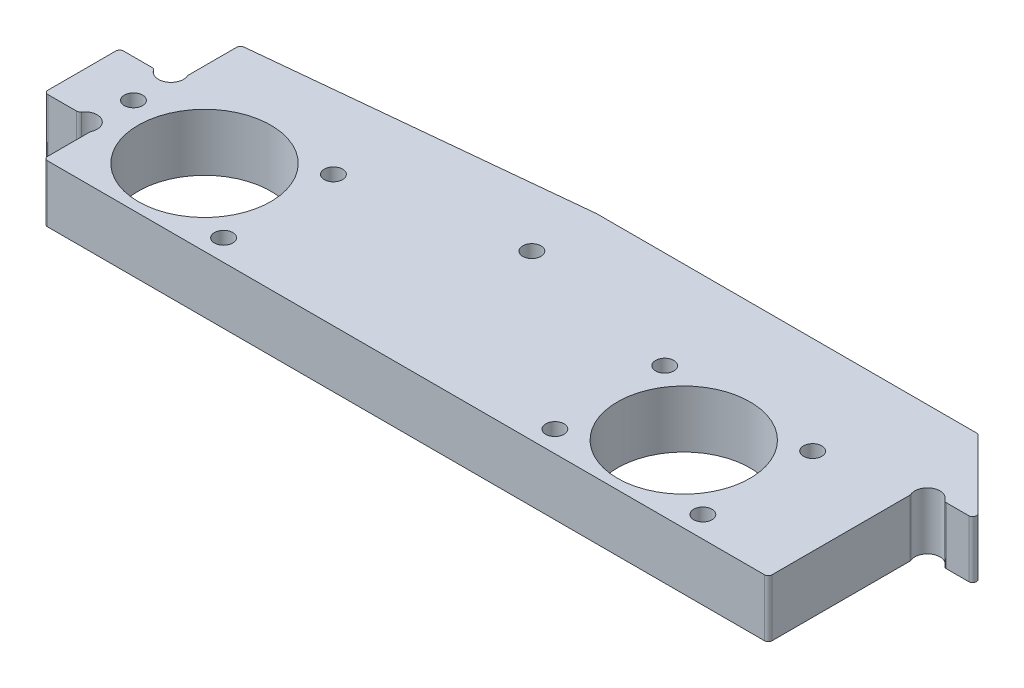
SolidWorks part; units mm, degrees
material "PE High Density"
ref_plane "Front Plane" through (0, 0, 0) normal (0, 0, 1) x (1, 0, 0)
ref_plane "Top Plane" through (0, 0, 0) normal (0, 1, 0) x (1, 0, 0)
ref_plane "Right Plane" through (0, 0, 0) normal (1, 0, 0) x (0, 0, -1)
sketch "Sketch1" plane through (0, 0, 0) normal (0, 1, 0) x (1, 0, 0)
  line L1 (-63.5, -19.05) -> (63.5, -19.05)
  line L2 (-63.5, -19.05) -> (-63.5, 19.05)
  line L3 (-63.5, 19.05) -> (63.5, 19.05)
  line L4 (63.5, -19.05) -> (63.5, 19.05)
  line L5 (-63.5, -19.05) -> (63.5, 19.05) construction
  line L6 (-63.5, 19.05) -> (63.5, -19.05) construction
  point P0 (0, 0)
  dimension "D1" = 127
  dimension "D2" = 38.1
extrude "Boss-Extrude1" add sketch "Sketch1" along normal blind 9.525
sketch "Sketch3" plane through (0, 0, 0) normal (0, -1, 0) x (1, 0, 0)
  line L0 (0, -19.05) -> (-63.5, -12.7)
  line L1 (63.5, -19.05) -> (-63.5, -19.05) construction
  line L2 (-63.5, -19.05) -> (-63.5, 19.05) construction
  line L3 (-63.5, -12.7) -> (-63.5, -19.05)
  line L4 (-63.5, -19.05) -> (0, -19.05)
  dimension "D1" = 6.35
extrude "Cut-Extrude2" cut sketch "Sketch3" against normal through all
sketch "Sketch4" plane through (0, 9.525, 0) normal (0, 1, 0) x (1, 0, 0)
  line L0 (-63.5, -6.35) -> (-39.9034, -6.35) construction
  line L1 (-63.5, 12.7) -> (-63.5, -19.05) construction
  line L2 (-39.9034, -6.35) -> (-39.9034, -19.05) construction
  line L3 (-63.5, -19.05) -> (63.5, -19.05) construction
  line L4 (39.9034, -6.35) -> (39.9034, -19.05) construction
  line L5 (39.9034, -6.35) -> (63.5, -6.35) construction
  line L6 (63.5, -19.05) -> (63.5, 19.05) construction
  circle A0 centre (-39.9034, -6.35) radius 2.2225
  circle A1 centre (39.9034, -6.35) radius 2.2225
  dimension "D3" = 4.445
  dimension "D1" = 12.7
  dimension "D2" = 23.5966
extrude "Cut-Extrude3" cut sketch "Sketch4" against normal through all
sketch "Sketch5" plane through (0, 9.525, 0) normal (0, 1, 0) x (1, 0, 0)
  circle A0 centre (-39.9034, -6.35) radius 3.1115
  circle A1 centre (39.9034, -6.35) radius 3.1115
  dimension "D1" = 6.223
extrude "Cut-Extrude4" cut sketch "Sketch5" against normal blind 2.5
sketch "Sketch7" plane through (0, 0, 0) normal (0, -1, 0) x (1, 0, 0)
  line L0 (58.7375, -14.2875) -> (58.7375, 14.2875) construction
  line L1 (58.7375, 14.2875) -> (-58.7375, 14.2875) construction
  line L2 (-58.7375, 14.2875) -> (-58.7375, -7.9375) construction
  line L3 (63.5, 14.2875) -> (58.7375, 14.2875) construction
  line L4 (63.5, 19.05) -> (63.5, -19.05) construction
  line L5 (58.7375, 14.2875) -> (58.7375, 19.05) construction
  line L6 (-63.5, 19.05) -> (63.5, 19.05) construction
  line L7 (-58.7375, 14.2875) -> (-63.5, 14.2875) construction
  line L8 (-63.5, -12.7) -> (-63.5, 19.05) construction
  line L9 (58.7375, -14.2875) -> (58.7375, -19.05) construction
  line L10 (63.5, -19.05) -> (0, -19.05) construction
  line L11 (-63.5, -12.7) -> (-58.7375, -12.7) construction
  line L12 (-58.7375, -12.7) -> (-58.7375, -7.9375) construction
  circle A0 centre (58.7375, 14.2875) radius 1.3891 construction
  circle A1 centre (58.7375, -14.2875) radius 1.3891 construction
  circle A2 centre (-58.7375, -7.9375) radius 1.3891
  circle A3 centre (-58.7375, 14.2875) radius 1.3891
  dimension "D1" = 2.7781
  dimension "D2" = 4.7625
extrude "Cut-Extrude6" cut sketch "Sketch7" against normal through all
sketch "Sketch8" plane through (0, 9.525, 0) normal (0, 1, 0) x (1, 0, 0)
  circle A0 centre (-39.9034, -6.35) radius 11.0363
  circle A1 centre (39.9034, -6.35) radius 11.0363
  dimension "D1" = 22.0726
extrude "Cut-Extrude7" cut sketch "Sketch8" against normal through all
sketch "Sketch9" plane through (0, 9.525, 0) normal (0, 1, 0) x (1, 0, 0)
  line L5 (0, 8.255) -> (0, 19.05) construction
  circle A6 centre (0, 8.255) radius 1.524
  dimension "D1" = 3.048
  dimension "D3" = 10.795
extrude "Cut-Extrude8" cut sketch "Sketch9" against normal through all
sketch "Sketch10" plane through (0, 9.525, 0) normal (0, 1, 0) x (1, 0, 0)
  line L6 (63.5, -19.05) -> (63.5, 19.05)
  line L7 (63.5, 19.05) -> (76.2, 6.35)
  line L8 (76.2, 6.35) -> (76.2, -19.05)
  line L9 (76.2, -19.05) -> (63.5, -19.05)
  dimension "D1" = 12.7
  dimension "D2" = 45
extrude "Boss-Extrude3" add sketch "Sketch10" against normal through all
sketch "Sketch11" plane through (0, 9.525, 0) normal (0, 1, 0) x (1, 0, 0)
  line L0 (71.4375, -19.05) -> (71.4375, -14.2875) construction
  line L1 (-63.5, -19.05) -> (76.2, -19.05) construction
  line L2 (71.4375, -14.2875) -> (76.2, -14.2875) construction
  line L3 (76.2, -19.05) -> (76.2, 6.35) construction
  line L4 (76.2, 1.5875) -> (71.4375, 1.5875) construction
  line L5 (71.4375, 1.5875) -> (71.4375, 6.35) construction
  line L6 (-58.7375, -14.2875) -> (-58.7375, -19.05) construction
  circle A0 centre (71.4375, 1.5875) radius 1.3891
  circle A1 centre (71.4375, -14.2875) radius 1.3891
  circle A2 centre (-58.7375, -14.2875) radius 1.3891 construction
extrude "Cut-Extrude9" cut sketch "Sketch11" against normal through all
sketch "Sketch13" plane through (0, 9.525, 0) normal (0, 1, 0) x (1, 0, 0)
  line L1 (-63.5, -19.05) -> (-53.975, -19.05)
  line L2 (-63.5, -19.05) -> (-63.5, -14.2875)
  line L3 (-63.5, 12.7) -> (-53.975, 12.7) construction
  line L5 (-63.5, -19.05) -> (-53.975, 12.7) construction
  line L6 (-63.5, 12.7) -> (-53.975, -19.05) construction
  line L7 (-58.7375, -14.2875) -> (-58.7375, -3.175) construction
  line L8 (-63.5, -14.2875) -> (-50.8, -14.2875) construction
  line L9 (-63.5, 12.7) -> (-63.5, 3.1115)
  line L10 (-63.5, 12.7) -> (-63.5, -19.05) construction
  line L11 (-63.5, 3.1115) -> (-53.975, 3.1115)
  line L12 (-53.975, 3.1115) -> (-53.975, 12.7)
  line L13 (-53.975, -19.05) -> (-53.975, -9.4615)
  line L14 (-53.975, -9.4615) -> (-63.5, -9.4615)
  line L15 (-63.5, -9.4615) -> (-63.5, -14.2875)
  line L16 (0, 19.05) -> (-63.5, 12.7) construction
  line L17 (-53.975, 12.7) -> (-53.975, 13.6525)
  line L18 (-53.975, 13.6525) -> (-63.5, 12.7)
  point P4 (-58.7375, -3.175)
  dimension "D1" = 12.7
  dimension "D2" = 12.573
extrude "Cut-Extrude10" cut sketch "Sketch13" against normal through all
sketch "Sketch14" plane through (0, 9.525, 0) normal (0, 1, 0) x (1, 0, 0)
  line L0 (-53.975, 3.1115) -> (-55.8605, 4.0259) construction
  line L1 (-55.8605, 4.0259) -> (-53.975, 4.9403) construction
  line L2 (-53.975, 3.1115) -> (-53.975, 13.6525) construction
  line L3 (-53.975, -9.4615) -> (-55.8605, -10.3759) construction
  line L4 (-55.8605, -10.3759) -> (-53.975, -11.2903) construction
  line L5 (-53.975, -19.05) -> (-53.975, -9.4615) construction
  line L6 (-53.975, 4.9403) -> (-53.975, 3.1115) construction
  line L7 (-53.975, -11.2903) -> (-53.975, -9.4615) construction
  circle A0 centre (-55.8605, 4.0259) radius 2.0955
  circle A1 centre (-55.8605, -10.3759) radius 2.0955
  dimension "D1" = 4.191
  dimension "D2" = 1.8288
extrude "Cut-Extrude11" cut sketch "Sketch14" against normal through all
sketch "Sketch15" plane through (0, 9.525, 0) normal (0, 1, 0) x (1, 0, 0)
  line L0 (-53.975, -19.05) -> (76.2, -19.05) construction
  line L5 (76.2, 6.477) -> (66.675, 6.477)
  line L6 (76.2, 6.477) -> (76.2, -19.05)
  line L11 (76.2, -19.05) -> (66.675, -19.05)
  line L12 (66.675, 6.477) -> (66.675, -19.05)
  line L13 (76.2, 6.477) -> (66.675, -19.05) construction
  line L14 (76.2, -19.05) -> (66.675, 6.477) construction
  line L15 (76.2, -19.05) -> (76.2, 6.35) construction
  point P4 (71.4375, -6.2865)
  point P8 (63.3976, 6.477)
  dimension "D1" = 9.525
  dimension "D2" = 25.527
extrude "Cut-Extrude12" cut sketch "Sketch15" against normal through all
sketch "Sketch16" plane through (0, 9.525, 0) normal (0, 1, 0) x (1, 0, 0)
  line L0 (66.675, 6.477) -> (68.5605, 5.5626) construction
  line L1 (68.5605, 5.5626) -> (66.675, 4.6482) construction
  line L2 (66.675, 6.477) -> (66.675, -19.05) construction
  circle A0 centre (68.5605, 5.5626) radius 2.0955
  dimension "D1" = 4.191
  dimension "D2" = 1.8288
extrude "Cut-Extrude13" cut sketch "Sketch16" against normal through all
sketch "Sketch17" plane through (0, 9.525, 0) normal (0, 1, 0) x (1, 0, 0)
  line L0 (-39.9034, -6.35) -> (-54.9129, -3.175) construction
  line L1 (-27.5844, 2.7937) -> (-39.9034, -6.35) construction
  line L2 (-39.9034, -6.35) -> (-27.5844, -15.4937) construction
  line L3 (27.5844, -15.4937) -> (39.9034, -6.35) construction
  line L4 (39.9034, -6.35) -> (52.2224, 2.7937) construction
  line L5 (27.5844, 2.7937) -> (39.9034, -6.35) construction
  line L6 (39.9034, -6.35) -> (52.2224, -15.4937) construction
  line L7 (-27.5844, -15.4937) -> (-27.5844, 2.7937) construction
  line L8 (27.5844, -15.4937) -> (27.5844, 2.7937) construction
  line L9 (27.5844, 2.7937) -> (52.2224, 2.7937) construction
  line L10 (52.2224, 2.7937) -> (52.2224, -15.4937) construction
  line L11 (-63.5, -3.175) -> (-54.9129, -3.175) construction
  line L12 (-63.5, 3.1115) -> (-63.5, -9.4615) construction
  circle A0 centre (-54.9129, -3.175) radius 1.524
  circle A1 centre (-27.5844, 2.7937) radius 1.524
  circle A2 centre (-27.5844, -15.4937) radius 1.524
  circle A3 centre (27.5844, -15.4937) radius 1.524
  circle A4 centre (27.5844, 2.7937) radius 1.524
  circle A5 centre (52.2224, 2.7937) radius 1.524
  circle A6 centre (52.2224, -15.4937) radius 1.524
  circle A7 centre (-39.9034, -6.35) radius 11.0363 construction
  circle A8 centre (39.9034, -6.35) radius 11.0363 construction
  point P18 (27.1493, -14.6922)
  dimension "D2" = 3.048
  dimension "D1" = 15.3416
  dimension "D3" = 24.638
extrude "Cut-Extrude14" cut sketch "Sketch17" against normal through all
fillet "Fillet1" radius 0.635 14 edges at (0, 4.7625, -19.05) (63.5, 4.7625, -19.05) (-53.975, 4.7625, 11.2903) (-57.7459, 4.7625, 9.4615) (-57.7459, 4.7625, -3.1115) (-53.975, 4.7625, -4.9403) (-53.975, 4.7625, 19.05) (-63.5, 4.7625, 9.4615) (-63.5, 4.7625, -3.1115) (-53.975, 4.7625, -13.6525) (76.073, 4.7625, -6.477) (70.4459, 4.7625, -6.477) (66.675, 4.7625, -4.6482) (66.675, 4.7625, 19.05)
